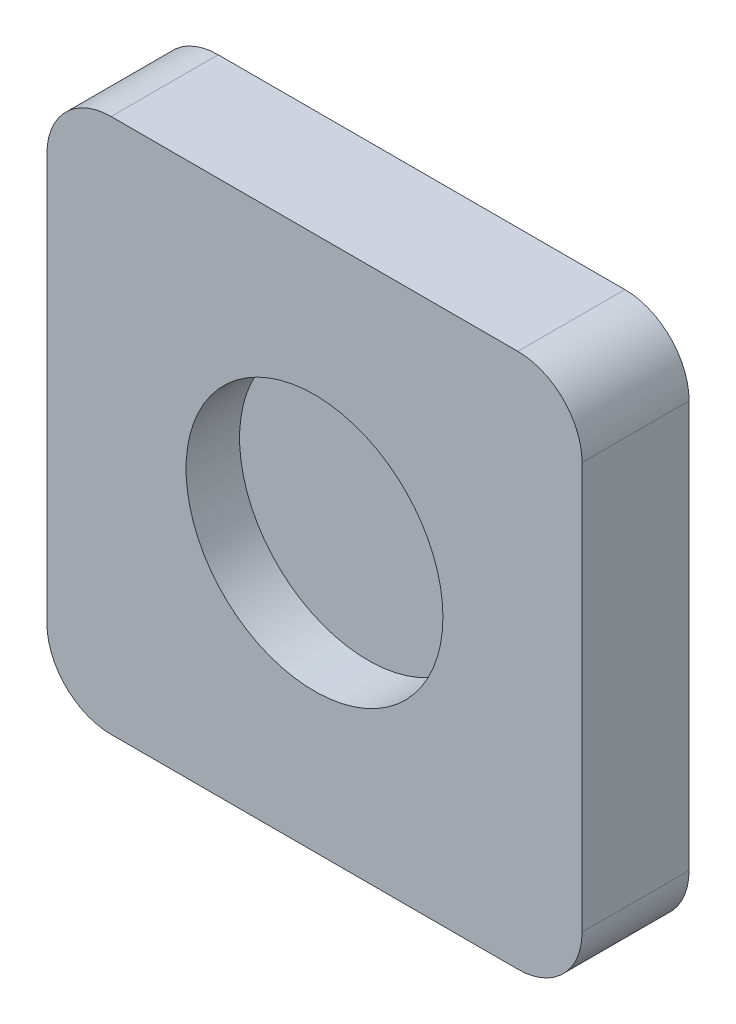
SolidWorks part; units mm, degrees
ref_plane "Front Plane" through (0, 0, 0) normal (0, 0, 1) x (1, 0, 0)
ref_plane "Top Plane" through (0, 0, 0) normal (0, 1, 0) x (1, 0, 0)
ref_plane "Right Plane" through (0, 0, 0) normal (1, 0, 0) x (0, 0, -1)
sketch "Sketch1" plane through (0, 0, 0) normal (0, 0, 1) x (1, 0, 0)
  line L1 (-0.095, -0.125) -> (0.095, -0.125)
  line L2 (-0.125, -0.095) -> (-0.125, 0.095)
  line L3 (-0.095, 0.125) -> (0.095, 0.125)
  line L4 (0.125, -0.095) -> (0.125, 0.095)
  line L5 (-0.125, -0.125) -> (0.125, 0.125) construction
  line L6 (-0.125, 0.125) -> (0.125, -0.125) construction
  arc A0 (-0.125, -0.095) -> (-0.095, -0.125) centre (-0.095, -0.095) ccw
  arc A1 (0.095, -0.125) -> (0.125, -0.095) centre (0.095, -0.095) ccw
  arc A2 (0.095, 0.125) -> (0.125, 0.095) centre (0.095, 0.095) cw
  arc A3 (-0.095, 0.125) -> (-0.125, 0.095) centre (-0.095, 0.095) ccw
  point P0 (0, 0)
  dimension "D3" = 0.03
  dimension "D1" = 0.25
  dimension "D2" = 0.25
extrude "Boss-Extrude1" add sketch "Sketch1" along normal blind 0.05
sketch "Sketch2" plane through (0, 0, 0.05) normal (0, 0, 1) x (1, 0, 0)
  circle A4 centre (0, 0) radius 0.06
  dimension "D1" = 0.12
extrude "Cut-Extrude1" cut sketch "Sketch2" against normal blind 0.025
